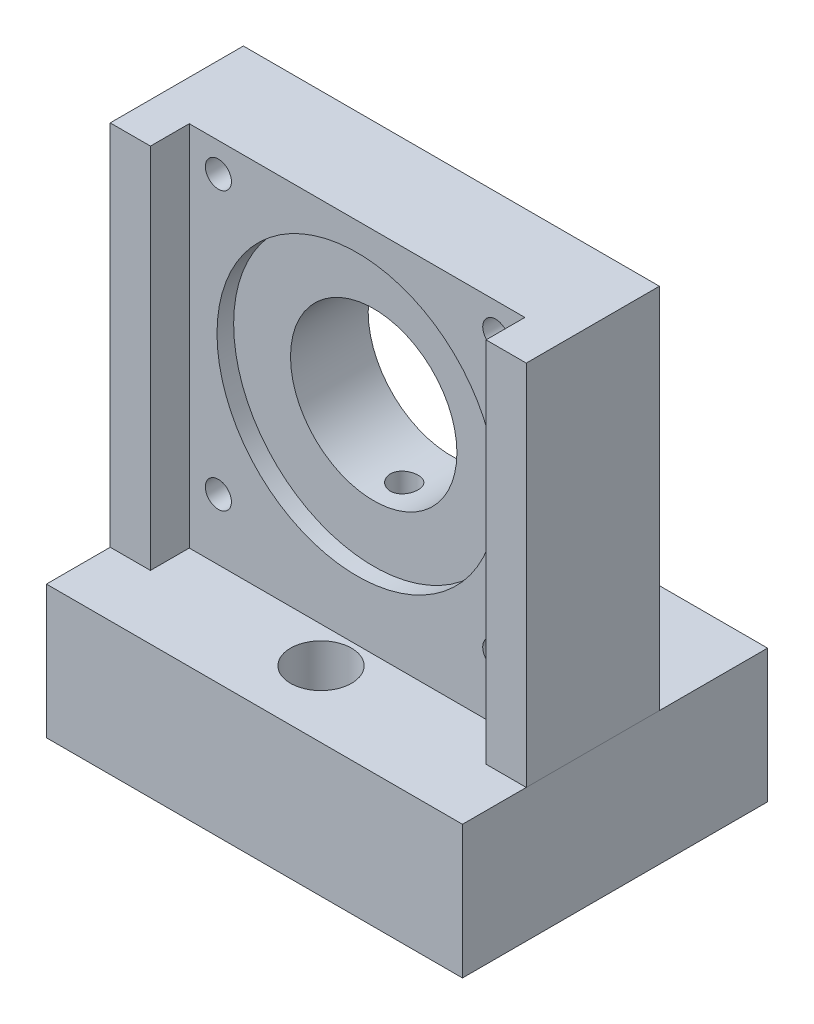
SolidWorks part; units mm, degrees
ref_plane "Front Plane" through (0, 0, 0) normal (0, 0, 1) x (1, 0, 0)
ref_plane "Top Plane" through (0, 0, 0) normal (0, 1, 0) x (1, 0, 0)
ref_plane "Right Plane" through (0, 0, 0) normal (1, 0, 0) x (0, 0, -1)
sketch "Sketch1" plane through (0, 0, 0) normal (0, 0, 1) x (1, 0, 0)
  line L0 (-37.5, -36) -> (-37.5, -60) construction
  line L1 (-37.5, -36) -> (37.5, -36)
  line L2 (-37.5, -36) -> (-37.5, 36)
  line L3 (-37.5, 36) -> (37.5, 36)
  line L4 (37.5, -36) -> (37.5, 36)
  line L5 (-37.5, -36) -> (37.5, 36) construction
  line L6 (-37.5, 36) -> (37.5, -36) construction
  point P0 (0, 0)
  dimension "D1" = 75
  dimension "D2" = 24
  dimension "D3" = 60
extrude "Boss-Extrude1" add sketch "Sketch1" along normal mid plane 24
sketch "Sketch3" plane through (0, 0, 12) normal (0, 0, 1) x (1, 0, 0)
  line L1 (30.25, -30.25) -> (-30.25, -30.25)
  line L2 (30.25, -30.25) -> (30.25, 30.25)
  line L3 (30.25, 30.25) -> (-30.25, 30.25)
  line L4 (-30.25, -30.25) -> (-30.25, 30.25)
  line L5 (30.25, -30.25) -> (-30.25, 30.25) construction
  line L6 (30.25, 30.25) -> (-30.25, -30.25) construction
  point P0 (0, 0)
  dimension "D1" = 60.5
extrude "Cut-Extrude2" cut sketch "Sketch3" against normal blind 7
sketch "Sketch2" plane through (0, 0, 5) normal (0, 0, 1) x (1, 0, 0)
  circle A0 centre (0, 0) radius 25.25
  dimension "D1" = 50.5
extrude "Cut-Extrude1" cut sketch "Sketch2" against normal blind 3
sketch "Sketch4" plane through (0, 0, 2) normal (0, 0, 1) x (1, 0, 0)
  circle A0 centre (0, 0) radius 15
  dimension "D1" = 30
extrude "Cut-Extrude3" cut sketch "Sketch4" against normal blind 29
sketch "Sketch5" plane through (0, 0, 0) normal (0, 0, 1) x (1, 0, 0)
  line L0 (-37.5, 36) -> (-37.5, -36) construction
  line L1 (37.5, -60) -> (-37.5, -60)
  line L2 (37.5, -60) -> (37.5, -30.25)
  line L3 (37.5, -30.25) -> (-37.5, -30.25)
  line L4 (-37.5, -60) -> (-37.5, -30.25)
  line L5 (37.5, -60) -> (-37.5, -30.25) construction
  line L6 (37.5, -30.25) -> (-37.5, -60) construction
  line L8 (-30.25, -30.25) -> (30.25, -30.25) construction
  line L9 (37.5, -36) -> (37.5, 36) construction
  point P0 (0, -45.125)
  dimension "D1" = 60
extrude "Boss-Extrude2" add sketch "Sketch5" along normal mid plane 134
sketch "Sketch6" plane through (0, 0, 12) normal (0, 0, 1) x (1, 0, 0)
  line L0 (37.5, -30.25) -> (37.5, 36) construction
  line L1 (-37.5, 36) -> (37.5, 36)
  line L2 (-37.5, 36) -> (-37.5, 30.25)
  line L3 (-37.5, 30.25) -> (37.5, 30.25)
  line L4 (37.5, 36) -> (37.5, 30.25)
  line L5 (30.25, 30.25) -> (-30.25, 30.25) construction
extrude "Cut-Extrude4" cut sketch "Sketch6" against normal mid plane 134
sketch "Sketch15" plane through (0, -30.25, 0) normal (0, 1, 0) x (1, 0, 0)
  line L0 (-37.5, 12) -> (37.5, 12) construction
  line L1 (37.5, 12) -> (37.5, 67) construction
  line L2 (37.5, 67) -> (-37.5, 67) construction
  line L3 (-37.5, 67) -> (-37.5, 12) construction
  line L4 (-30.25, -5) -> (-30.25, -12) construction
  line L5 (-30.25, -12) -> (-37.5, -12) construction
  line L6 (-37.5, -12) -> (-37.5, -67) construction
  line L7 (-37.5, -67) -> (37.5, -67) construction
  line L8 (37.5, -67) -> (37.5, -12) construction
  line L9 (37.5, -12) -> (30.25, -12) construction
  line L10 (30.25, -12) -> (30.25, -5) construction
  line L11 (30.25, -5) -> (-30.25, -5) construction
  line L12 (-37.5, 12) -> (37.5, 12)
  line L13 (37.5, 12) -> (37.5, 67)
  line L14 (37.5, 67) -> (-37.5, 67)
  line L15 (-37.5, 67) -> (-37.5, 12)
  line L16 (-30.25, -5) -> (-30.25, -12)
  line L17 (-30.25, -12) -> (-37.5, -12)
  line L18 (-37.5, -12) -> (-37.5, -67)
  line L19 (-37.5, -67) -> (37.5, -67)
  line L20 (37.5, -67) -> (37.5, -12)
  line L21 (37.5, -12) -> (30.25, -12)
  line L22 (30.25, -12) -> (30.25, -5)
  line L23 (30.25, -5) -> (-30.25, -5)
extrude "Cut-Extrude12" cut sketch "Sketch15" against normal blind 5.75
sketch "Sketch7" plane through (0, -36, 0) normal (0, 1, 0) x (1, 0, 0)
  line L0 (0, -5) -> (0, -11.5) construction
  line L2 (-17.5, 12) -> (-17.5, 19.5) construction
  line L4 (-17.5, 12) -> (0, 12) construction
  line L5 (37.5, 12) -> (-37.5, 12) construction
  line L6 (0, -11.5) -> (-17.5, -11.5) construction
  line L7 (-17.5, -11.5) -> (-17.5, 12) construction
  line L8 (-25.25, -5) -> (25.25, -5) construction
  circle A0 centre (-17.5, 19.5) radius 3.2
  circle A1 centre (0, -11.5) radius 3.2
  circle A2 centre (17.5, 19.5) radius 3.2
  point P2 (0, 0)
  point P7 (-17.5, 12)
  point P8 (-17.5, 19.5)
  point P16 (0, 0)
  point P18 (0, 0)
  point P20 (0, 0)
  dimension "D4" = 6.4
  dimension "D1" = 6.5
  dimension "D2" = 31
  dimension "D3" = 17.5
extrude "Cut-Extrude5" cut sketch "Sketch7" against normal mid plane 134
sketch "Sketch9" plane through (0, -36, 0) normal (0, 1, 0) x (1, 0, 0)
  line L1 (-37.5, 31.5) -> (37.5, 31.5)
  line L2 (-37.5, 31.5) -> (-37.5, -23.5)
  line L3 (-37.5, -23.5) -> (37.5, -23.5)
  line L4 (37.5, 31.5) -> (37.5, -23.5)
  line L6 (-17.5, 19.5) -> (-17.5, 31.5) construction
  line L7 (0, -11.5) -> (0, -23.5) construction
  line L8 (-37.5, 67) -> (-37.5, 12) construction
  line L9 (37.5, -67) -> (37.5, -12) construction
  dimension "D1" = 12
extrude "Cut-Extrude7" cut sketch "Sketch9" against normal through all flip side to cut
sketch "Sketch8" plane through (0, -36, 0) normal (0, 1, 0) x (1, 0, 0)
  circle A0 centre (-17.5, 19.5) radius 5.5
  circle A1 centre (17.5, 19.5) radius 5.5
  circle A2 centre (0, -11.5) radius 5.5
  dimension "D1" = 11
extrude "Cut-Extrude6" cut sketch "Sketch8" against normal blind 13
sketch "Sketch10" plane through (0, 0, 5) normal (0, 0, 1) x (1, 0, 0)
  line L1 (25, -25) -> (-25, -25) construction
  line L2 (25, -25) -> (25, 25) construction
  line L3 (25, 25) -> (-25, 25) construction
  line L4 (-25, -25) -> (-25, 25) construction
  line L5 (25, -25) -> (-25, 25) construction
  line L6 (25, 25) -> (-25, -25) construction
  circle A0 centre (-25, 25) radius 2.35
  circle A1 centre (25, 25) radius 2.35
  circle A2 centre (25, -25) radius 2.35
  circle A3 centre (-25, -25) radius 2.35
  point P0 (0, 0)
  dimension "D1" = 4.7
  dimension "D2" = 50
extrude "Cut-Extrude8" cut sketch "Sketch10" against normal through all
sketch "Sketch11" plane through (0, -60, 0) normal (0, -1, 0) x (1, 0, 0)
  line L1 (-27.35, -12) -> (-22.65, -12) construction
  line L3 (37.5, 5) -> (-37.5, 5) construction
  line L4 (37.5, 5) -> (37.5, -12) construction
  line L5 (37.5, -12) -> (-37.5, -12) construction
  line L6 (-37.5, 5) -> (-37.5, -12) construction
  line L8 (37.5, -12) -> (37.5, 12) construction
  line L9 (-37.5, -12) -> (-37.5, 12) construction
  line L10 (-37.5, 5) -> (37.5, -12) construction
  line L11 (-37.5, -3.5) -> (37.5, -3.5) construction
  line L12 (-37.5, 23.5) -> (-37.5, -31.5) construction
  line L13 (0, -3.5) -> (0, -12) construction
  line L15 (30.25, 5) -> (-30.25, 5) construction
  circle A0 centre (-19, -3.5) radius 2.5
  circle A1 centre (19, -3.5) radius 2.5
  circle A2 centre (0, -3.5) radius 2.5
  point P12 (0, -3.5)
  dimension "D1" = 5
  dimension "D2" = 19
extrude "Cut-Extrude9" cut sketch "Sketch11" against normal blind 54
sketch "Sketch12" plane through (0, -60, 0) normal (0, -1, 0) x (1, 0, 0)
  circle A0 centre (-19, -3.5) radius 3.2
  circle A1 centre (0, -3.5) radius 3.2
  circle A2 centre (19, -3.5) radius 3.2
  dimension "D1" = 6.4
extrude "Cut-Extrude10" cut sketch "Sketch12" against normal up to surface (24 mm away) up to face at (-5.5, -36, 11.5)
sketch "Sketch13" plane through (0, -60, 0) normal (0, -1, 0) x (1, 0, 0)
  circle A0 centre (-19, -3.5) radius 5.5
  circle A1 centre (0, -3.5) radius 5.5
  circle A2 centre (19, -3.5) radius 5.5
  dimension "D1" = 11
extrude "Cut-Extrude11" cut sketch "Sketch13" against normal blind 15
sketch "Sketch14" plane through (37.5, 0, 0) normal (1, 0, 0) x (0, 0, -1)
  line L0 (-23.5, -36) -> (31.5, -36)
  line L1 (31.5, -60) -> (31.5, -36) construction
  point P2 (0, 0)
  point P3 (-23.5, -36)
split "Split1" trim tools "Sketch14" bodies to split 113 resulting bodies 114 115
